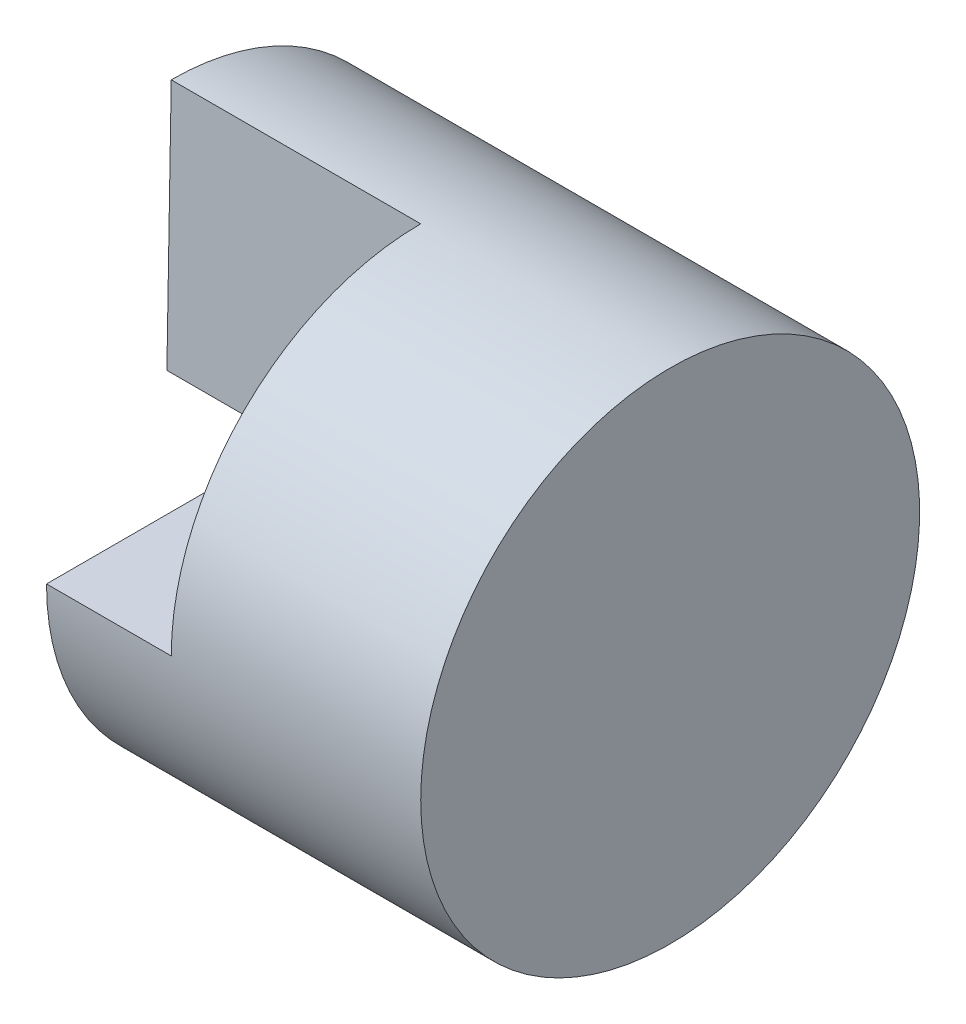
SolidWorks part; units mm, degrees
ref_plane "Front Plane" through (0, 0, 0) normal (0, 0, 1) x (1, 0, 0)
ref_plane "Top Plane" through (0, 0, 0) normal (0, 1, 0) x (1, 0, 0)
ref_plane "Right Plane" through (0, 0, 0) normal (1, 0, 0) x (0, 0, -1)
sketch "Sketch5" plane through (0, 0, 0) normal (0, 0, 1) x (1, 0, 0)
  line L0 (0, 0) -> (4, 0)
  dimension "D1" = 4
revolve "Revolve-Thin2" add sketch "Sketch5" angle 360 about L0 wall 2
sketch "Sketch6" plane through (0, 0, 0) normal (0, 0, 1) x (1, 0, 0)
  line L1 (0, 2) -> (1, 2)
  line L2 (0, 2) -> (0, 0)
  line L3 (0, 0) -> (1, 0)
  line L4 (1, 2) -> (1, 0)
  line L5 (4, 2) -> (3, 2)
  line L6 (4, 2) -> (4, 0)
  line L7 (4, 0) -> (3, 0)
  line L8 (3, 2) -> (3, 0)
  dimension "D1" = 1
  dimension "D2" = 1
  dimension "D3" = 2
  dimension "D4" = 2
extrude "Cut-Extrude5" cut sketch "Sketch6" against normal blind 11 contours L5 L8 L7 L6 | L4 L1 L2 L3
sketch "Sketch8" plane through (0, 0, 0) normal (0, 0, -1) x (-1, 0, 0)
  line L0 (0, 0) -> (-1, 0) construction
  line L1 (0, 2) -> (-0.5, 2)
  line L2 (0, 2) -> (0, 0)
  line L3 (0, 0) -> (-0.5, 0)
  line L4 (-0.5, 2) -> (-0.5, 0)
extrude "Cut-Extrude7" cut sketch "Sketch8" against normal blind 10
sketch "Sketch9" plane through (0, 0, 0) normal (0, 0, -1) x (-1, 0, 0)
  line L0 (-1, 2) -> (-3, 2) construction
  line L5 (-0.5, 0) -> (-2, 0)
  line L6 (-0.5, 0) -> (-0.5, 2)
  line L7 (-0.5, 2) -> (-2, 2)
  line L8 (-2, 0) -> (-2, 2)
  line L9 (-4, 2) -> (-4, 0) construction
  dimension "D1" = 2
extrude "Cut-Extrude8" cut sketch "Sketch9" against normal blind 10
sketch "Sketch10" plane through (4, 0, 0) normal (1, 0, 0) x (0, 0, -1)
  line L0 (2, 0) -> (-0.035, 0)
  line L1 (-0.035, 0) -> (0, 2)
  arc A0 (0, 2) -> (2, 0) centre (0, 0) cw
extrude "Boss-Extrude1" add sketch "Sketch10" against normal blind 4
sketch "Sketch13" plane through (0, 0, 0) normal (-1, 0, 0) x (0, 0, 1)
  line L1 (2, 0) -> (-2.4499, 0)
  line L2 (2, 0) -> (2, -3.1982)
  line L3 (2, -3.1982) -> (-2.4499, -3.1982)
  line L4 (-2.4499, 0) -> (-2.4499, -3.1982)
extrude "Cut-Extrude10" cut sketch "Sketch13" against normal blind 1
